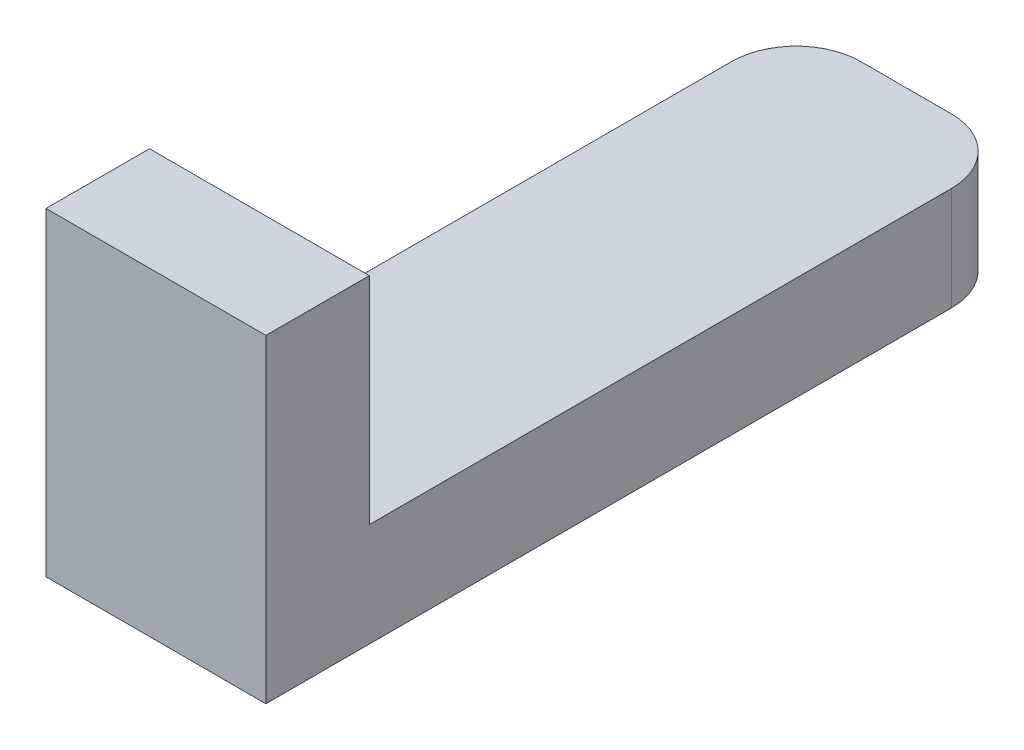
SolidWorks part; units mm, degrees
ref_plane "Front Plane" through (0, 0, 0) normal (0, 0, 1) x (1, 0, 0)
ref_plane "Top Plane" through (0, 0, 0) normal (0, 1, 0) x (1, 0, 0)
ref_plane "Right Plane" through (0, 0, 0) normal (1, 0, 0) x (0, 0, -1)
sketch "Sketch1" plane through (0, 0, 0) normal (1, 0, 0) x (0, 0, -1)
  line L0 (-22.098, 0) -> (0, 0)
  line L1 (0, 0) -> (0, 3.048)
  line L2 (0, 3.048) -> (-19.05, 3.048)
  line L3 (-19.05, 3.048) -> (-19.05, 9.398)
  line L4 (-19.05, 9.398) -> (-22.098, 9.398)
  line L5 (-22.098, 9.398) -> (-22.098, 0)
  point P3 (0, 0)
  dimension "D1" = 3.048
  dimension "D2" = 6.35
  dimension "D3" = 19.05
  dimension "D4" = 3.048
extrude "Boss-Extrude1" add sketch "Sketch1" along normal blind 6.477
fillet "Fillet1" radius 1.905 2 edges at (0, 1.524, 0) (6.477, 1.524, 0)
